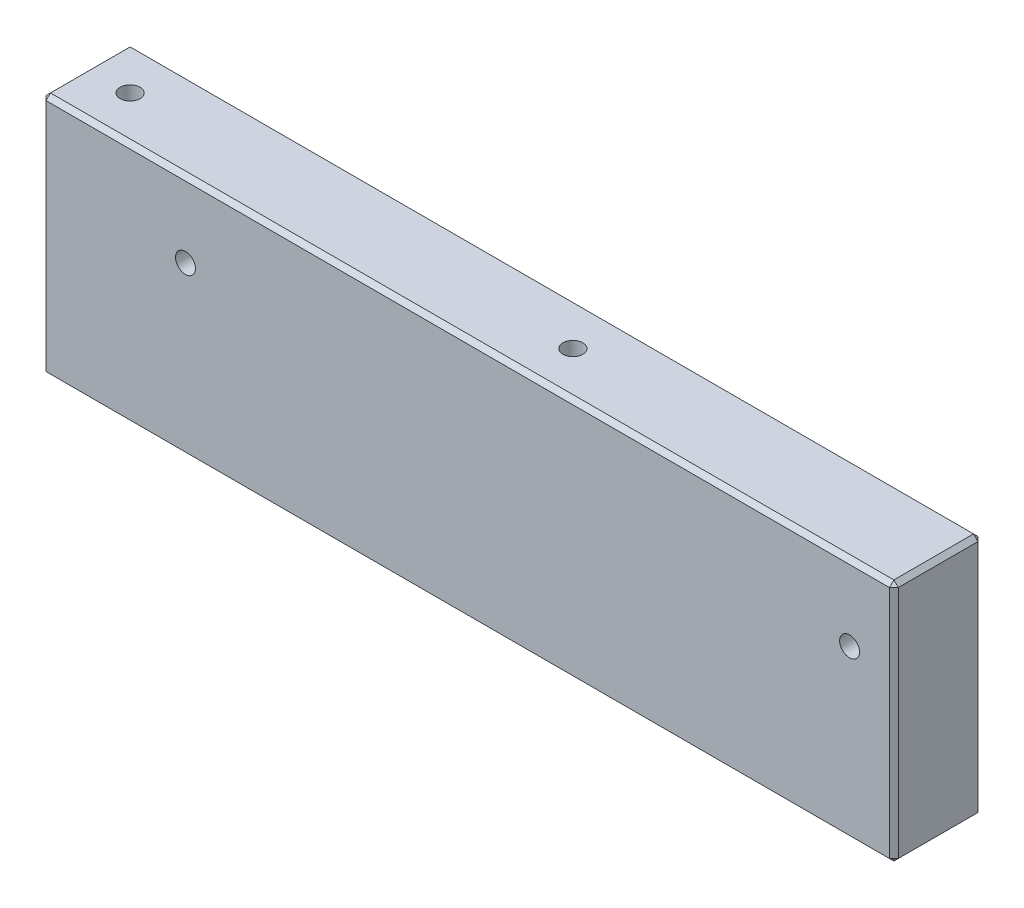
SolidWorks part; units mm, degrees
ref_plane "Front Plane" through (0, 0, 0) normal (0, 0, 1) x (1, 0, 0)
ref_plane "Top Plane" through (0, 0, 0) normal (0, 1, 0) x (1, 0, 0)
ref_plane "Right Plane" through (0, 0, 0) normal (1, 0, 0) x (0, 0, -1)
ref_plane "Plane1" through (0, 0, 0) normal (0, 0, -1) x (-1, 0, 0)
sketch "Sketch1" plane through (0, 0, 0) normal (0, 0, -1) x (-1, 0, 0)
  line L0 (0, 55) -> (-192.5, 55)
  line L1 (-192.5, 55) -> (-192.5, 0)
  line L2 (-192.5, 0) -> (0, 0)
  line L3 (0, 0) -> (0, 55)
extrude "Boss-Extrude1" add sketch "Sketch1" against normal blind 20
hole_wizard "CBORE for M4 Hex Head Machine Screw1" positions "Sketch3" profile "Sketch2" counterbore size "M4" standard "ANSI Metric"
sketch "Sketch3" plane through (0, 0, 0) normal (0, -1, 0) x (-1, 0, 0)
  point P0 (-110, -10)
  point P1 (-10, -10)
sketch "Sketch2" plane through (110, 0, 10) normal (1, 0, 0) x (0, 0, -1)
  line L0 (0, 0) -> (0, 55)
  line L1 (0, 55) -> (2.25, 55)
  line L3 (2.25, 55) -> (2.25, 50)
  line L4 (2.25, 50) -> (4.5, 50)
  line L5 (4.5, 50) -> (4.5, 0)
  line L7 (4.5, 0) -> (0, 0)
  line L11 (0, -6.35) -> (0, 107.95) construction
  dimension "Thru Hole Dia." = 4.5
  dimension "Thru Hole Depth" = 55
  dimension "C'Bore Dia." = 9
  dimension "C'Bore Depth" = 50
hole_wizard "CBORE for M4 Hex Head Machine Screw2" positions "Sketch5" profile "Sketch4" counterbore size "M4" standard "ANSI Metric"
sketch "Sketch5" plane through (0, 0, 0) normal (0, 0, -1) x (-1, 0, 0)
  point P0 (-182.5, 38)
  point P1 (-32.5, 38)
sketch "Sketch4" plane through (182.5, 38, 0) normal (1, 0, 0) x (0, 1, 0)
  line L0 (0, 0) -> (0, 20)
  line L1 (0, 20) -> (2.25, 20)
  line L3 (2.25, 20) -> (2.25, 5)
  line L4 (2.25, 5) -> (4.5, 5)
  line L5 (4.5, 5) -> (4.5, 0)
  line L7 (4.5, 0) -> (0, 0)
  line L11 (0, -6.35) -> (0, 107.95) construction
  dimension "Thru Hole Dia." = 4.5
  dimension "Thru Hole Depth" = 20
  dimension "C'Bore Dia." = 9
  dimension "C'Bore Depth" = 5
chamfer "Chamfer1" distance 1 angle 45 12 edges at (96.25, 55, 0) (192.5, 27.5, 0) (0, 55, 10) (192.5, 55, 10) (96.25, 55, 20) (96.25, 0, 0) (0, 27.5, 0) (192.5, 0, 10) (0, 27.5, 20) (192.5, 27.5, 20) (0, 0, 10) (96.25, 0, 20)
